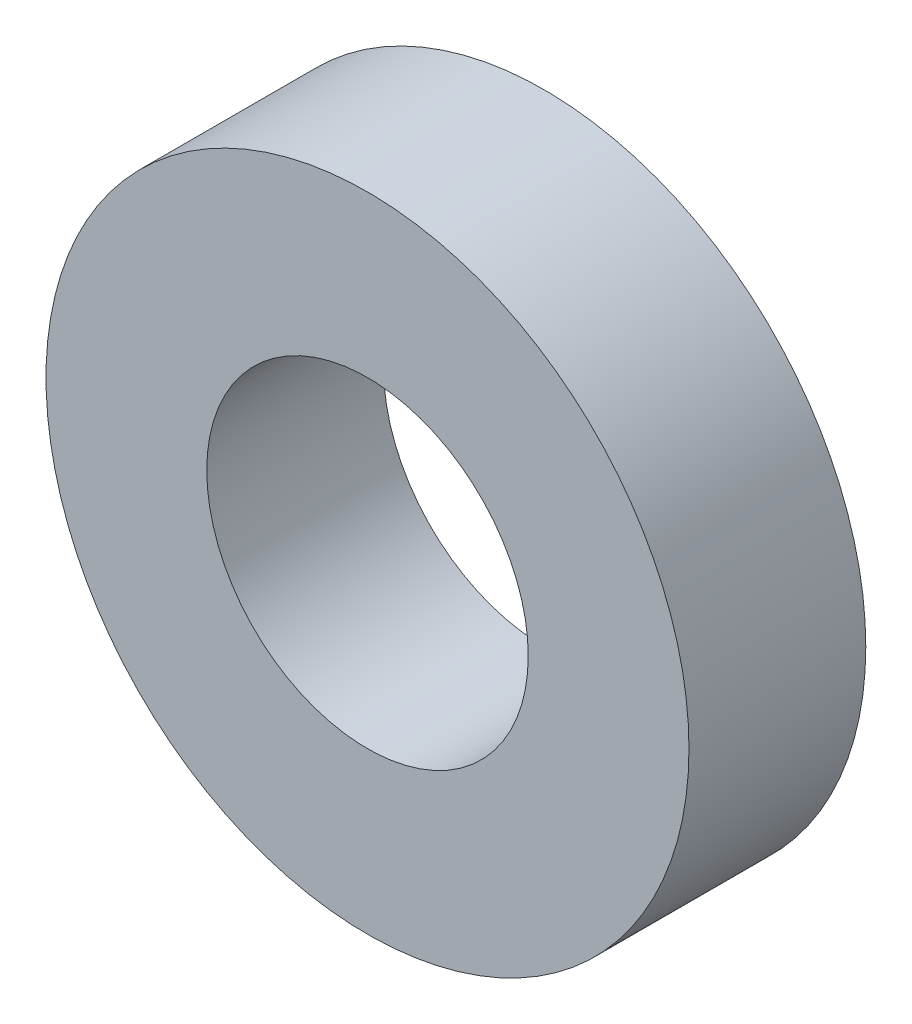
SolidWorks part; units mm, degrees
ref_plane "前视基准面" through (0, 0, 0) normal (0, 0, 1) x (1, 0, 0)
ref_plane "上视基准面" through (0, 0, 0) normal (0, 1, 0) x (1, 0, 0)
ref_plane "右视基准面" through (0, 0, 0) normal (1, 0, 0) x (0, 0, -1)
other "Configuration Table"
sketch "草图1" plane through (0, 0, 0) normal (0, 0, 1) x (1, 0, 0)
  circle A0 centre (0, 0) radius 10
  circle A1 centre (0, 0) radius 5
  dimension "D1" = 20
  dimension "D2" = 10
extrude "凸台-拉伸1" add sketch "草图1" along normal blind 5.5
